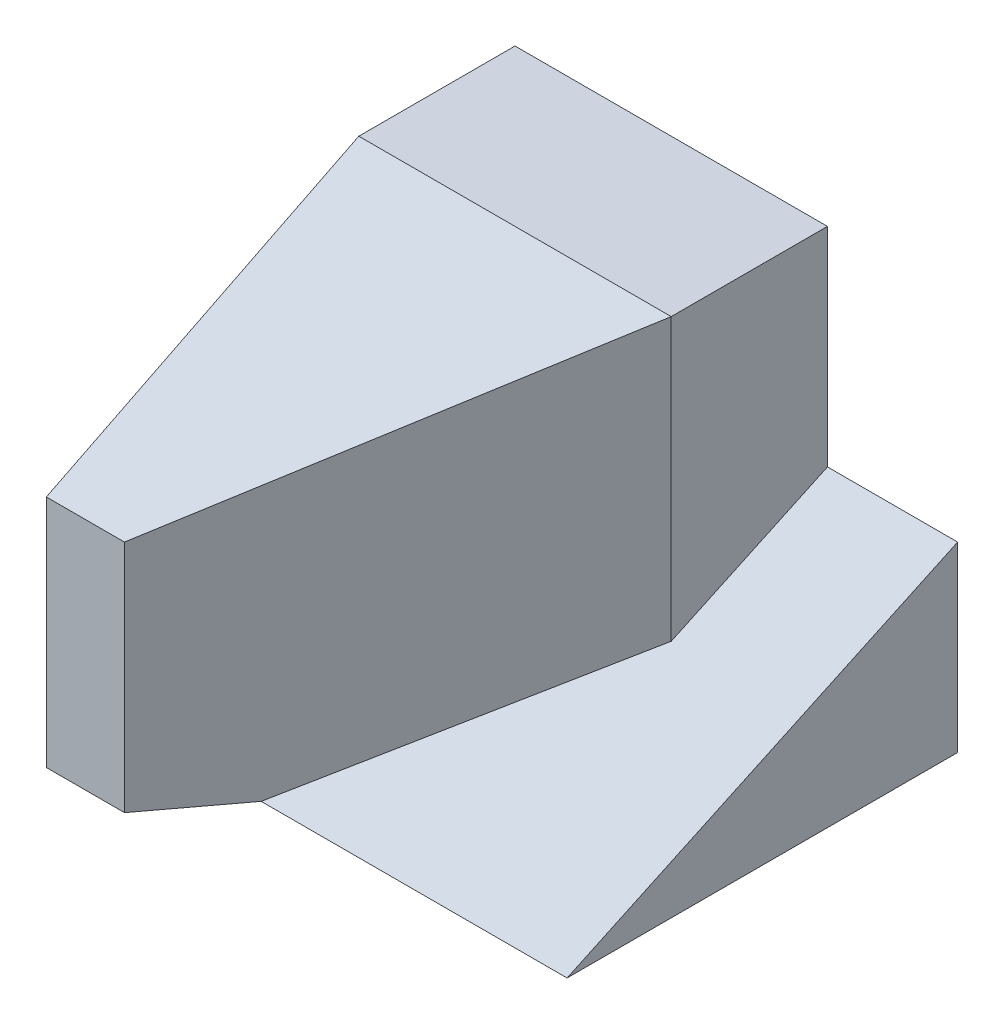
SolidWorks part; units mm, degrees
ref_plane "Front Plane" through (0, 0, 0) normal (0, 0, 1) x (1, 0, 0)
ref_plane "Top Plane" through (0, 0, 0) normal (0, 1, 0) x (1, 0, 0)
ref_plane "Right Plane" through (0, 0, 0) normal (1, 0, 0) x (0, 0, -1)
sketch "Sketch1" plane through (0, 0, 0) normal (0, 1, 0) x (1, 0, 0)
  line L1 (0, 0) -> (60, 0)
  line L2 (0, 0) -> (0, 90)
  line L3 (0, 90) -> (60, 90)
  line L4 (60, 0) -> (60, 90)
  dimension "D1" = 90
  dimension "D2" = 60
extrude "Extrude1" add sketch "Sketch1" along normal blind 75
sketch "Sketch2" plane through (60, 0, 0) normal (1, 0, 0) x (0, 0, -1)
  line L0 (60, 75) -> (0, 45)
  line L1 (0, 75) -> (90, 75) construction
  line L2 (0, 75) -> (0, 0) construction
  line L3 (0, 45) -> (0, 75)
  line L4 (0, 75) -> (60, 75)
  dimension "D1" = 60
  dimension "D2" = 45
extrude "Extrude2" cut sketch "Sketch2" against normal through all
sketch "Sketch3" plane through (0, 75, 0) normal (0, 1, 0) x (1, 0, 0)
  line L0 (60, 60) -> (15, 0)
  line L1 (60, 60) -> (60, 90) construction
  line L2 (0, 0) -> (60, 0) construction
  line L3 (15, 0) -> (60, 0)
  line L4 (60, 0) -> (60, 60)
  dimension "D1" = 15
  dimension "D2" = 60
extrude "Extrude3" cut sketch "Sketch3" against normal through all
sketch "Sketch4" plane through (60, 0, 0) normal (1, 0, 0) x (0, 0, -1)
  line L0 (90, 0) -> (15, 0)
  line L1 (15, 0) -> (90, 35)
  line L2 (90, 75) -> (90, 0) construction
  line L3 (90, 35) -> (90, 0)
  dimension "D1" = 35
  dimension "D2" = 75
extrude "Extrude4" add sketch "Sketch4" along normal blind 25 and the other way blind 55
